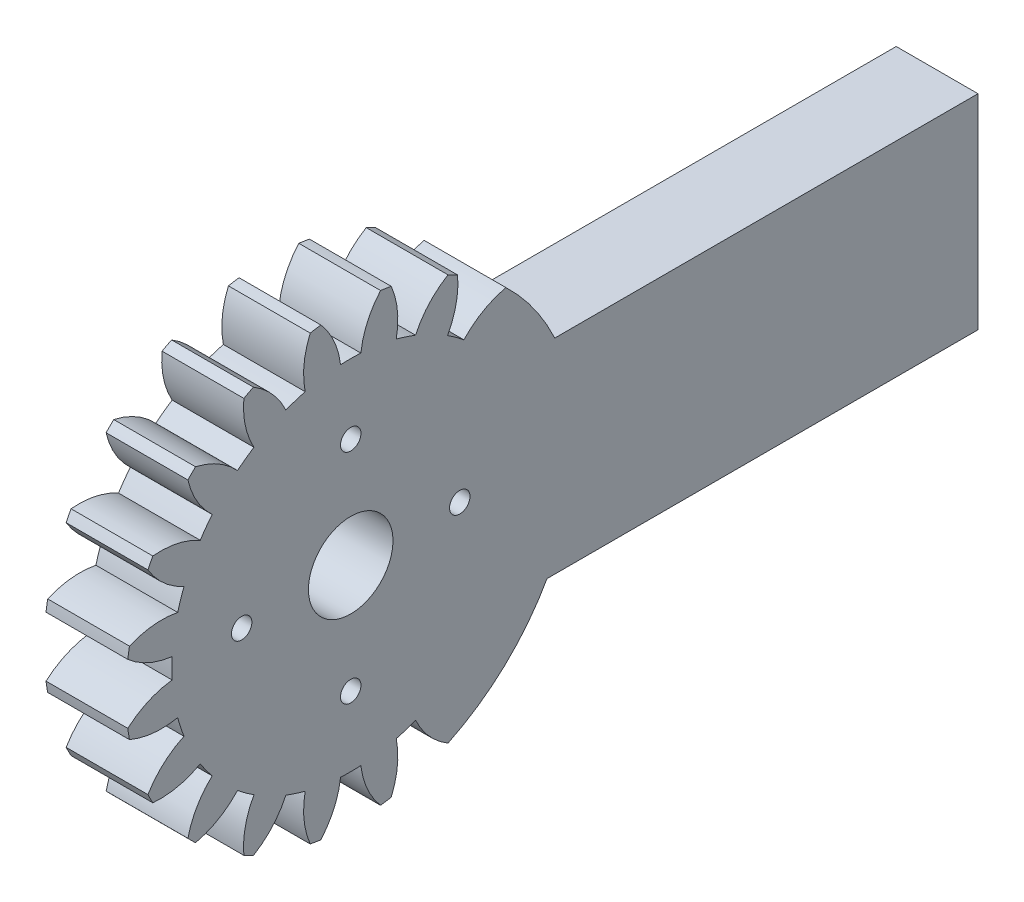
SolidWorks part; units mm, degrees
ref_plane "Plane1" through (0, 0, 0) normal (0, 0, 1) x (1, 0, 0)
ref_plane "Plane2" through (0, 0, 0) normal (0, 1, 0) x (1, 0, 0)
ref_plane "Plane3" through (0, 0, 0) normal (1, 0, 0) x (0, 0, -1)
sketch "HoldingSke" plane through (0, 0, 0) normal (0, 1, 0) x (1, 0, 0)
  line L0 (0, 0) -> (0.6265, -0.228)
  line L1 (-15, 0) -> (100, 0) construction
  line L2 (0, 0) -> (-2.1039, 2.3779)
  line L3 (0, 0) -> (-11.863, 4.5341)
  line L4 (0, 0) -> (8.1152, 2.9537)
  line L5 (0, 0) -> (-46.8476, -17.4728)
  line L6 (0, 0) -> (-4.9738, -3.3558)
  line L7 (-2.1039, 2.3779) -> (8.6586, 51.2059)
  line L8 (-76.2, 54.61) -> (-74.4, 54.61)
  line L9 (-71.009, 38.7566) -> (-53.1078, 45.2721)
  line L10 (-76.2, 71.12) -> (104.1128, 71.12)
  line L11 (0, 0) -> (-6, 0)
  line L12 (-76.2, 101.6) -> (-76.147, 101.6)
  line L13 (24.9733, 27.94) -> (52.9518, 28.4284)
  line L14 (24.9733, 27.94) -> (24.9743, 27.94)
  line L15 (24.9733, 27.94) -> (100.4006, 29.5858)
  line L16 (-63.627, -1.5) -> (-12.827, -1.5)
  circle A0 centre (0, 0) radius 5
  circle A1 centre (0, 0) radius 13.124
  circle A2 centre (0, 0) radius 37.5
  circle A3 centre (0, 0) radius 5
  dimension "MHD" = 26.248
  dimension "Hub_dia" = 75
  dimension "Bore" = 10
  dimension "MBD" = 10
  dimension "Num_teeth" = 20
  dimension "Pitch" = 0.6667
  dimension "Overall_len" = 50
  dimension "Show_teeth" = 20
  dimension "Thickness" = 6
  dimension "OAL" = 50.0001
  dimension "T_dim" = 1.8
  dimension "Ap" = 20
  dimension "H" = 19.05
  dimension "Pitch_radius" = 180.3128
  dimension "Width" = 6
  dimension "Backlash" = 0.053
  dimension "Addendum_fac" = 1
  dimension "Dedendum_fac" = 1.25
  dimension "Clearance_fac" = 0.25
  dimension "Dedendum_add" = 0.001
  dimension "Module" = 1.5
sketch "BasProSke" plane through (0, 0, 0) normal (0, 1, 0) x (1, 0, 0)
  line L0 (-10, 0) -> (60, 0) construction
  line L1 (0, 0) -> (0, 16.5)
  line L2 (0, 0) -> (6, 0)
  line L3 (6, 0) -> (6, 16.5)
  line L4 (6, 16.5) -> (0, 16.5)
  dimension "Thickness" = 6
  dimension "Diameter" = 33
revolve "Base-Revolve" add sketch "BasProSke" angle 360 about L0
sketch "TooCutSke" plane through (0, 0, 0) normal (1, 0, 0) x (0, 0, -1)
  line L1 (0, 0) -> (0, 107) construction
  line L2 (0, 0) -> (-1.2696, 14.9462) construction
  line L3 (0, 0) -> (-4.6808, 29.5532) construction
  line L4 (-1.2696, 14.9462) -> (-2.3404, 14.7766) construction
  arc A0 (0.7438, 13.1029) -> (-0.7438, 13.1029) centre (0, 0) ccw
  arc A1 (2.21, 16.377) -> (-2.21, 16.377) centre (0, 0) ccw
  circle A2 centre (0, 0) radius 15 construction
  circle A3 centre (0, 0) radius 14.0954 construction
  arc A4 (-0.7438, 13.1029) -> (-2.21, 16.377) centre (-6.7025, 12.3999) ccw
  arc A5 (2.21, 16.377) -> (0.7438, 13.1029) centre (6.7025, 12.3999) ccw
  dimension "Root_dia" = 26.248
  dimension "Overcut_dia" = 33.0508
  dimension "Pitch_dia" = 30
  dimension "Base_dia" = 28.1908
  dimension "Flank_rad" = 6
  dimension "Half_ang" = 9
  dimension "Half_CT" = 1.0841
extrude "ToothCut" cut sketch "TooCutSke" along normal through all
fillet "Breaks" [suppressed] radius 0.03
fillet "RootFillets" [suppressed] radius 0.376
pattern_circular "TeethCuts" count 20 every 18 about axis through (-10, 0, 0) along (1, 0, 0) skipping 12, 13, 14, 15, 16, 17 of "ToothCut", "RootFillets", "Breaks"
sketch "HubNeaOneSke" plane through (0, 0, 0) normal (-1, 0, 0) x (0, 0, 1)
  circle A0 centre (0, 0) radius 13.124
  dimension "Diameter" = 26.248
extrude "HubNearOne" [suppressed] add sketch "HubNeaOneSke" along normal blind 44.0001
sketch "HubNeaBotSke" plane through (0, 0, 0) normal (-1, 0, 0) x (0, 0, 1)
  circle A0 centre (0, 0) radius 13.124
  dimension "Diameter" = 26.248
extrude "HubNearBoth" [suppressed] add sketch "HubNeaBotSke" along normal blind 22
ref_plane "FarPln" through (6, 0, 0) normal (1, 0, 0) x (0, 0, -1)
sketch "HubFarSke" plane through (6, 0, 0) normal (1, 0, 0) x (0, 0, -1)
  circle A0 centre (0, 0) radius 13.124
  dimension "Diameter" = 26.248
extrude "HubFar" [suppressed] add sketch "HubFarSke" along normal blind 22
sketch "BorSke" plane through (0, 0, 0) normal (1, 0, 0) x (0, 0, -1)
  circle A0 centre (0, 0) radius 3.1
  dimension "Diameter" = 6.2
extrude "Bore" cut sketch "BorSke" along normal mid plane 100.0001
sketch "KeySke" plane through (0, 0, 0) normal (1, 0, 0) x (0, 0, -1)
  line L0 (-2, 0) -> (-2, 6.8)
  line L1 (-2, 6.8) -> (2, 6.8)
  line L2 (2, 6.8) -> (2, 0)
  line L3 (0, 0) -> (0, 34) construction
  line L4 (-2, 0) -> (2, 0)
  dimension "Offset" = 6.8
  dimension "Width" = 4
extrude "Keyway" [suppressed] cut sketch "KeySke" along normal mid plane 100.0001
pattern_circular "Keyway2" [suppressed] count 2 every 90 about axis through (-10, 0, 0) along (1, 0, 0)
sketch "Esquisse2" plane through (6, 0, 0) normal (1, 0, 0) x (0, 0, -1)
  line L0 (11.4178, 6.9436) -> (46.0178, 6.9436)
  line L1 (11.4178, 6.9436) -> (11.4178, -8.0564)
  line L2 (46.0178, 6.9436) -> (46.0178, -8.0564)
  line L3 (11.4178, -8.0564) -> (46.0178, -8.0564)
  line L4 (-34.7493, 0) -> (83.9803, 0) construction
  dimension "D1" = 34.6
  dimension "D2" = 15
extrude "Boss.-Extru.1" add sketch "Esquisse2" against normal blind 6
sketch "Esquisse3" plane through (0, 0, 0) normal (-1, 0, 0) x (0, 0, 1)
  circle A0 centre (8, 0) radius 0.75
  circle A1 centre (0, 8) radius 0.75
  circle A2 centre (0, -8) radius 0.75
  circle A3 centre (-8, 0) radius 0.75
  circle A4 centre (0, 0) radius 3.1 construction
  dimension "D1" = 1.5
  dimension "D2" = 1.5
  dimension "D3" = 1.5
  dimension "D4" = 1.5
  dimension "D5" = 8
  dimension "D6" = 8
  dimension "D7" = 8
  dimension "D8" = 8
extrude "Enlèv. mat.-Extru.1" cut sketch "Esquisse3" against normal blind 6
equation "' \"Module@HoldingSke\" = 6.35"
equation "' \"Num_teeth@HoldingSke\" = 12"
equation "' \"Ap@HoldingSke\" =  20"
equation "' \"Ap@HoldingSke\" = 20"
equation "' \"Width@HoldingSke\" = 0.5 * 25.4"
equation "' \"Hub_dia@HoldingSke\"= 1 * 25.4"
equation "' \"Hub_dia@HoldingSke\" = 1 * 25.4"
equation "' \"Overall_len@HoldingSke\" = 1.0 * 25.4"
equation "' \"Bore@HoldingSke\" = 0.75 * 25.4"
equation "' \"T_dim@HoldingSke\" = 0.1 * 25.4"
equation "' \"Width@KeySke\" = 0.25 * 25.4"
equation "' \"Show_teeth@HoldingSke\" = 13"
equation "' \"Backlash@HoldingSke\" = 0.009 * 25.4"
equation "' \"Addendum_fac@HoldingSke\" = 1.0"
equation "' \"Dedendum_fac@HoldingSke\" = 1.25"
equation "' \"Dedendum_add@HoldingSke\" = 0.00005 * 25.4"
equation "' \"Clearance_fac@HoldingSke\" = 0.25"
equation "\"Pitch@HoldingSke\" = 1 / \"Module@HoldingSke\""
equation "\"Overcut_dia@TooCutSke\" = (\"Num_teeth@HoldingSke\" + 2 * \"Addendum_fac@HoldingSke\") / \"Pitch@HoldingSke\" + 0.002 * 25.4"
equation "\"Pitch_dia@TooCutSke\" = \"Num_teeth@HoldingSke\" / \"Pitch@HoldingSke\""
equation "\"Base_dia@TooCutSke\" = \"Num_teeth@HoldingSke\" / \"Pitch@HoldingSke\" * cos((\"Ap@HoldingSke\"  * 3.14159265 / 180))"
equation "\"Root_dia@TooCutSke\" = (\"Num_teeth@HoldingSke\" + 2) / \"Pitch@HoldingSke\" - 2 * (\"Addendum_fac@HoldingSke\" + \"Dedendum_fac@HoldingSke\") / \"Pitch@HoldingSke\" - \"Dedendum_add@HoldingSke\" * 2"
equation "\"Half_ang@TooCutSke\" = 180 / \"Num_teeth@HoldingSke\""
equation "\"Half_CT@TooCutSke\" = \"Num_teeth@HoldingSke\" / \"Pitch@HoldingSke\" * sin((3.14159265 / 2 / \"Num_teeth@HoldingSke\")) / 2 - 7 * \"Backlash@HoldingSke\" / 4"
equation "\"Flank_rad@TooCutSke\" = \"Num_teeth@HoldingSke\" / \"Pitch@HoldingSke\" / 5"
equation "\"Radius@RootFillets\" = \"Clearance_fac@HoldingSke\" / \"Pitch@HoldingSke\" + \"Dedendum_add@HoldingSke\""
equation "\"Break_rad@Breaks\" = 0.02 / \"Pitch@HoldingSke\""
equation "\"Thickness@HoldingSke\" = \"Width@HoldingSke\""
equation "\"OAL@HoldingSke\" = \"Thickness@HoldingSke\""
equation "\"MHD@HoldingSke\" = (\"Num_teeth@HoldingSke\" + 2) / \"Pitch@HoldingSke\" - 2 * (\"Addendum_fac@HoldingSke\" + \"Dedendum_fac@HoldingSke\")  / \"Pitch@HoldingSke\" - \"Dedendum_add@HoldingSke\" * 2"
equation "\"MBD@HoldingSke\" = (\"Num_teeth@HoldingSke\" + 2) / \"Pitch@HoldingSke\" - 2 * (\"Addendum_fac@HoldingSke\" + \"Dedendum_fac@HoldingSke\")  / \"Pitch@HoldingSke\" - \"Dedendum_add@HoldingSke\" * 2 - 0.002 * 25.4"
equation "\"MHD@HoldingSke\" = ((sgn( \"MHD@HoldingSke\" - \"Hub_dia@HoldingSke\" )-1)*( \"MHD@HoldingSke\" - \"Hub_dia@HoldingSke\" ))/-2+ \"Hub_dia@HoldingSke\""
equation "\"MBD@HoldingSke\" = ((sgn( \"MBD@HoldingSke\" - \"Bore@HoldingSke\" )-1)*( \"MBD@HoldingSke\" - \"Bore@HoldingSke\" ))/-2+ \"Bore@HoldingSke\""
equation "\"OAL@HoldingSke\" = ((sgn( \"OAL@HoldingSke\" - \"Overall_len@HoldingSke\" )+1)*( \"OAL@HoldingSke\" - \"Overall_len@HoldingSke\" ))/2 + \"Overall_len@HoldingSke\" + 0.000002 * 25.4"
equation "\"Num_teeth@TeethCuts\" = int( \"Show_teeth@HoldingSke\" ) + 1"
equation "\"Num_teeth@TeethCuts\" = ((sgn( \"Num_teeth@TeethCuts\" - \"Num_teeth@HoldingSke\" )-1)*( \"Num_teeth@TeethCuts\" - \"Num_teeth@HoldingSke\" ))/-2+ \"Num_teeth@HoldingSke\""
equation "\"Num_teeth@TeethCuts\" = ((sgn( \"Num_teeth@TeethCuts\" - 2.0)+1)*( \"Num_teeth@TeethCuts\" - 2.0))/2 +2.0"
equation "\"Angle@TeethCuts\" = 360.0 / \"Num_teeth@HoldingSke\""
equation "\"Diameter@BasProSke\" = (\"Num_teeth@HoldingSke\" + 2 * \"Addendum_fac@HoldingSke\") / \"Pitch@HoldingSke\""
equation "\"Thickness@BasProSke\"  = \"Thickness@HoldingSke\""
equation "' \"Fillet_rad@BasProSke\" =  \"Thickness@HoldingSke\" * 0.05"
equation "' \"Fillet_rad@BasProSke\" = \"Thickness@HoldingSke\" * 0.05"
equation "\"MHD@HoldingSke\" = ((sgn( \"MHD@HoldingSke\" - \"Root_dia@TooCutSke\" )-1)*( \"MHD@HoldingSke\" - \"Root_dia@TooCutSke\" ))/-2+ \"Root_dia@TooCutSke\""
equation "\"Diameter@HubNeaOneSke\" = \"MHD@HoldingSke\""
equation "\"Length@HubNearOne\" = \"OAL@HoldingSke\" - \"Thickness@BasProSke\""
equation "\"Diameter@HubNeaBotSke\" = \"MHD@HoldingSke\""
equation "\"Length@HubNearBoth\" = ( \"OAL@HoldingSke\" - \"Thickness@BasProSke\" ) / 2.0"
equation "\"Thickness@FarPln\" = \"Thickness@BasProSke\""
equation "\"Diameter@HubFarSke\" = \"MHD@HoldingSke\""
equation "\"Length@HubFar\" = ( \"OAL@HoldingSke\" - \"Thickness@BasProSke\" ) / 2.0"
equation "\"D1@Bore\" = \"OAL@HoldingSke\" * 2.0"
equation "\"D1@Keyway\" = \"OAL@HoldingSke\" * 2.0"
equation "\"Offset@KeySke\" = \"T_dim@HoldingSke\" + \"MBD@HoldingSke\" / 2.0"
